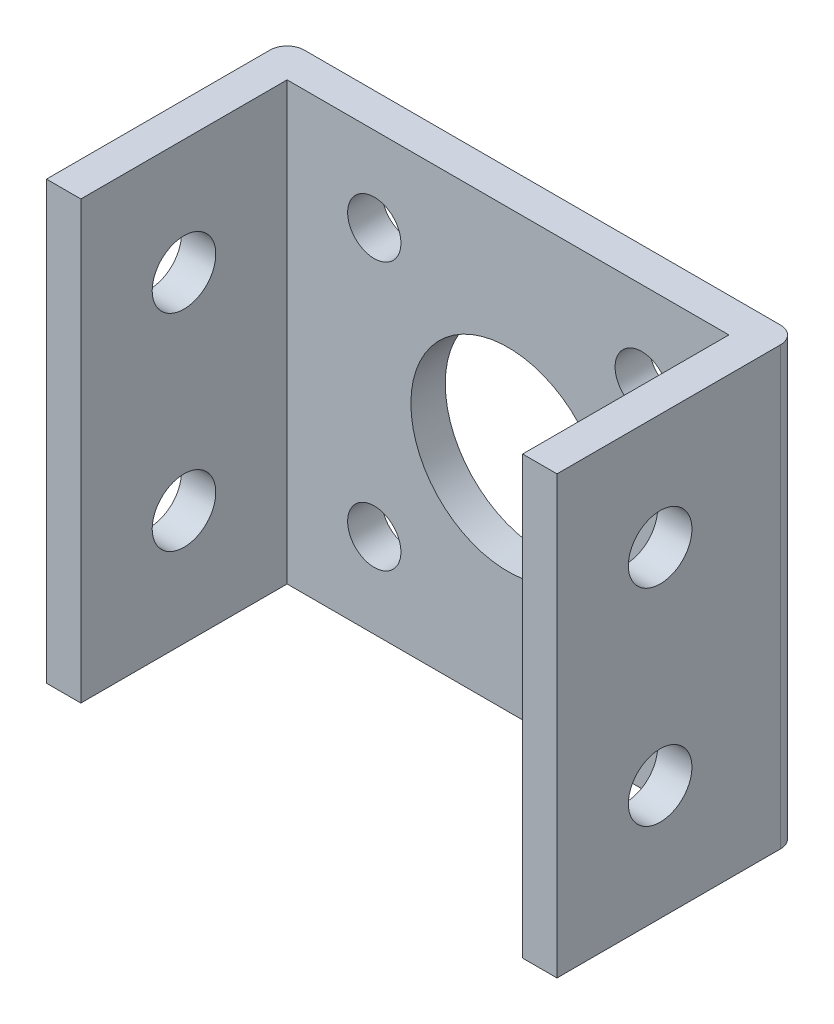
SolidWorks part; units mm, degrees
ref_plane "Front Plane" through (0, 0, 0) normal (0, 0, 1) x (1, 0, 0)
ref_plane "Top Plane" through (0, 0, 0) normal (0, 1, 0) x (1, 0, 0)
ref_plane "Right Plane" through (0, 0, 0) normal (1, 0, 0) x (0, 0, -1)
sketch "Sketch1" plane through (0, 0, 0) normal (0, 1, 0) x (1, 0, 0)
  line L0 (0, 0) -> (0, 31.75) construction
  line L1 (-14.85, 0) -> (14.85, 0)
  line L2 (14.85, 0) -> (14.85, -14)
  line L3 (14.85, -14) -> (12.85, -14)
  line L4 (12.85, -14) -> (12.85, -2)
  line L5 (12.85, -2) -> (-12.85, -2)
  line L6 (-12.85, -2) -> (-12.85, -14)
  line L7 (-12.85, -14) -> (-14.85, -14)
  line L8 (-14.85, -14) -> (-14.85, 0)
  dimension "D1" = 2
  dimension "D2" = 29.7
  dimension "D3" = 2
  dimension "D4" = 12
extrude "Boss-Extrude1" add sketch "Sketch1" along normal mid plane 25.4
sketch "Sketch2" plane through (-14.85, 0, 0) normal (-1, 0, 0) x (0, 0, 1)
  line L0 (0, 0) -> (21.026, 0) construction
  line L1 (0, 12.7) -> (0, -12.7) construction
  circle A0 centre (8, -6) radius 1.85
  circle A1 centre (8, 6) radius 1.85
  dimension "D1" = 3.7
  dimension "D2" = 12
  dimension "D3" = 8
extrude "Cut-Extrude1" cut sketch "Sketch2" against normal through all
sketch "Sketch3" plane through (0, 0, 0) normal (0, 0, -1) x (-1, 0, 0)
  circle A0 centre (0, 0) radius 5.65
  dimension "D1" = 11.3
extrude "Cut-Extrude2" cut sketch "Sketch3" against normal through all
sketch "Sketch4" plane through (0, 0, 2) normal (0, 0, 1) x (1, 0, 0)
  line L0 (0, 0) -> (0, 13.4152) construction
  line L1 (0, 0) -> (18.1171, 0) construction
  circle A0 centre (-7.78, 7.78) radius 1.55
  circle A1 centre (-7.78, -7.78) radius 1.55
  circle A2 centre (7.78, -7.78) radius 1.55
  circle A3 centre (7.78, 7.78) radius 1.55
  dimension "D3" = 3.1
  dimension "D1" = 15.56
  dimension "D2" = 15.56
extrude "Cut-Extrude3" cut sketch "Sketch4" against normal through all
fillet "Fillet1" radius 1 2 edges at (14.85, 0, 0) (-14.85, 0, 0)
